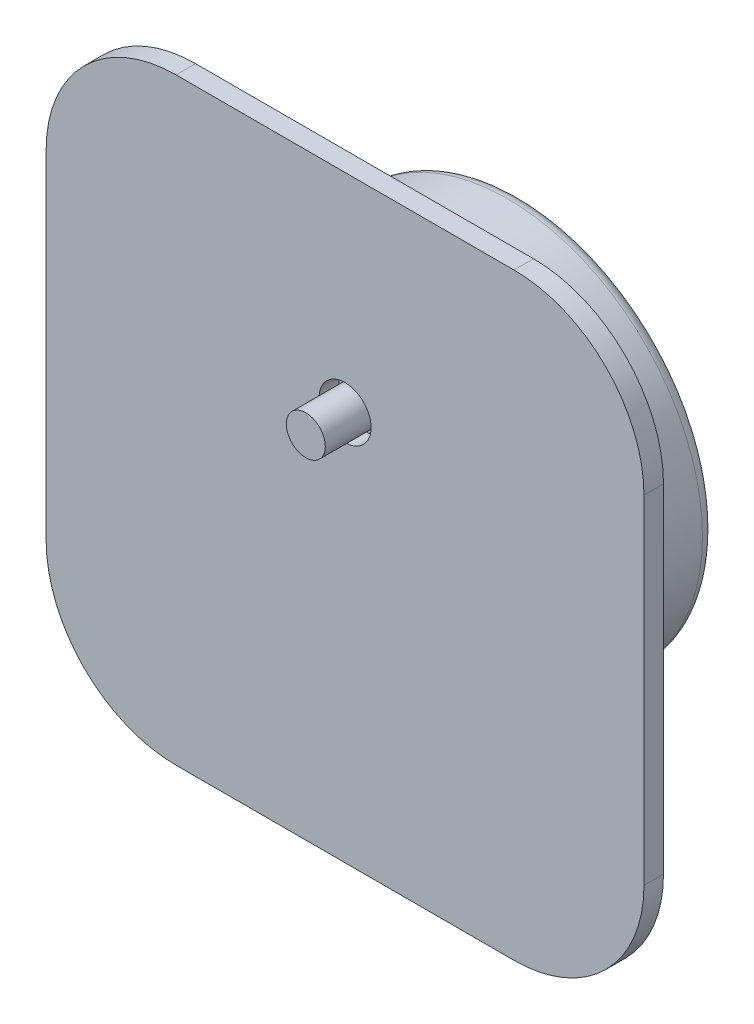
SolidWorks part; units mm, degrees
ref_plane "Front Plane" through (0, 0, 0) normal (0, 0, 1) x (1, 0, 0)
ref_plane "Top Plane" through (0, 0, 0) normal (0, 1, 0) x (1, 0, 0)
ref_plane "Right Plane" through (0, 0, 0) normal (1, 0, 0) x (0, 0, -1)
sketch "Sketch1" plane through (0, 0, 0) normal (0, 0, 1) x (1, 0, 0)
  line L1 (-23, -23) -> (23, -23)
  line L2 (-23, -23) -> (-23, 23)
  line L3 (-23, 23) -> (23, 23)
  line L4 (23, -23) -> (23, 23)
  line L5 (-23, -23) -> (23, 23) construction
  line L6 (-23, 23) -> (23, -23) construction
  circle A1 centre (0, 7) radius 2
  point P0 (0, 0)
  dimension "D3" = 4
  dimension "D1" = 46
  dimension "D2" = 46
  dimension "D4" = 7
extrude "Boss-Extrude1" add sketch "Sketch1" along normal blind 1.5
sketch "Sketch3" plane through (0, 0, 0) normal (0, 0, -1) x (-1, 0, 0)
  line L5 (16.0453, -5.5015) -> (13.9547, -5.5015)
  line L6 (16.0453, -5.5015) -> (16.0453, 5.5015)
  line L7 (16.0453, 5.5015) -> (13.9547, 5.5015)
  arc A0 (7.3521, -13.0746) -> (13.9547, -5.5015) centre (0, 0) ccw
  arc A1 (7.3521, -13.0746) -> (-7.3521, -13.0746) centre (0, 0) cw
  arc A2 (13.9547, 5.5015) -> (-7.3521, -13.0746) centre (0, 0) ccw
  point P1 (15, 0)
  point P3 (0, -15)
  dimension "D1" = 30
extrude "Boss-Extrude2" add sketch "Sketch3" along normal blind 12
fillet "Fillet1" radius 1 1 edges at (15, 0, -12)
sketch "Sketch4" plane through (0, 0, 0) normal (0, 0, 1) x (1, 0, 0)
  circle A0 centre (0, 7) radius 1.5
  dimension "D1" = 3
extrude "Boss-Extrude3" add sketch "Sketch4" along normal blind 4.52
fillet "Fillet2" radius 10 4 edges at (-23, -23, 0.75) (-23, 23, 0.75) (23, -23, 0.75) (23, 23, 0.75)
